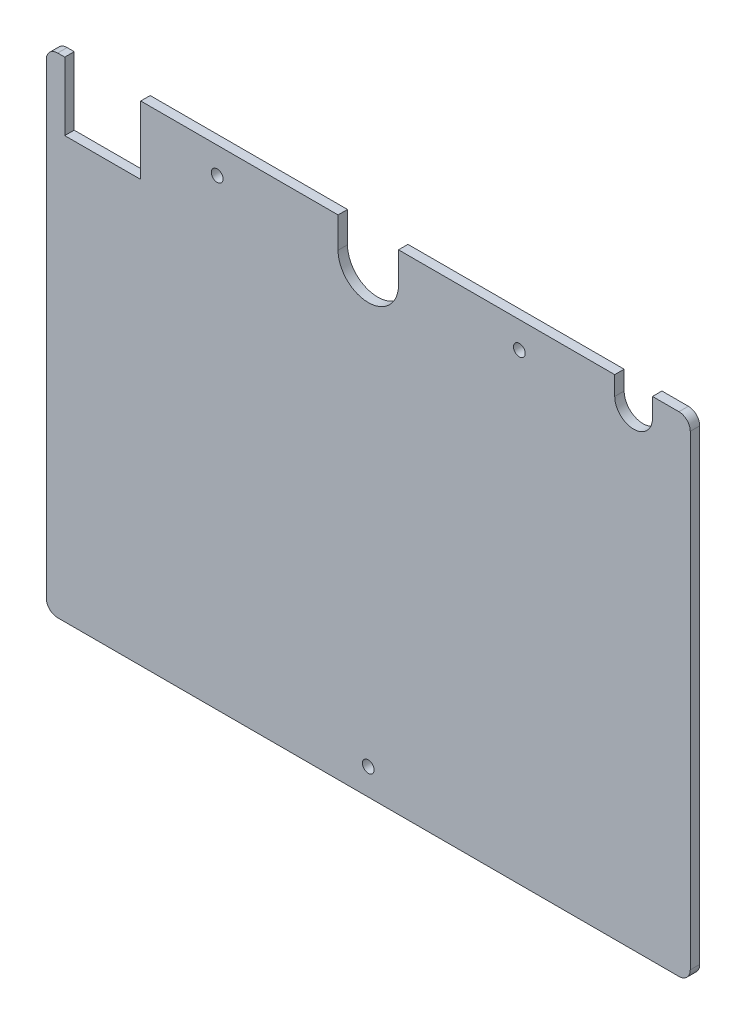
SolidWorks part; units mm, degrees
ref_plane "Plano frontal" through (0, 0, 0) normal (0, 0, 1) x (1, 0, 0)
ref_plane "Plano superior" through (0, 0, 0) normal (0, 1, 0) x (1, 0, 0)
ref_plane "Plano direito" through (0, 0, 0) normal (1, 0, 0) x (0, 0, -1)
sketch "Esboço1" plane through (0, 0, 0) normal (0, 0, 1) x (1, 0, 0)
  line L1 (-82.25, 64.75) -> (82.25, 64.75)
  line L2 (-85.25, 61.75) -> (-85.25, -61.75)
  line L3 (-82.25, -64.75) -> (82.25, -64.75)
  line L4 (85.25, 61.75) -> (85.25, -61.75)
  line L5 (-85.25, 64.75) -> (85.25, -64.75) construction
  line L6 (-85.25, -64.75) -> (85.25, 64.75) construction
  arc A0 (-85.25, -61.75) -> (-82.25, -64.75) centre (-82.25, -61.75) ccw
  arc A1 (82.25, -64.75) -> (85.25, -61.75) centre (82.25, -61.75) ccw
  arc A2 (82.25, 64.75) -> (85.25, 61.75) centre (82.25, 61.75) cw
  arc A3 (-82.25, 64.75) -> (-85.25, 61.75) centre (-82.25, 61.75) ccw
  point P0 (0, 0)
  dimension "D1" = 3
  dimension "D2" = 129.5
  dimension "D3" = 170.5
extrude "Ressalto-extrusão1" add sketch "Esboço1" along normal blind 2.5
sketch "Esboço2" plane through (0, 0, 2.5) normal (0, 0, 1) x (1, 0, 0)
  line L0 (8, 56.65) -> (8, 64.75)
  line L1 (82.25, 64.75) -> (-82.25, 64.75) construction
  line L2 (8, 64.75) -> (-8, 64.75)
  line L3 (-8, 64.75) -> (-8, 56.65)
  line L5 (-60.25, 64.75) -> (-80.3642, 64.75)
  line L6 (-60.25, 64.75) -> (-60.25, 46.75)
  line L7 (-60.25, 46.75) -> (-80.3642, 46.75)
  line L8 (-80.3642, 64.75) -> (-80.3642, 46.75)
  line L9 (85.25, -61.75) -> (85.25, 61.75) construction
  line L10 (65.25, 64.75) -> (75.25, 64.75)
  line L11 (65.25, 64.75) -> (65.25, 59.75)
  line L13 (75.25, 64.75) -> (75.25, 59.75)
  line L14 (-82.25, -64.75) -> (82.25, -64.75) construction
  line L15 (0, 0) -> (0, 27.1205) construction
  line L16 (-85.25, 61.75) -> (-85.25, -61.75) construction
  arc A0 (-8, 56.65) -> (8, 56.65) centre (0, 56.65) ccw
  arc A1 (65.25, 59.75) -> (75.25, 59.75) centre (70.25, 59.75) ccw
  circle A2 centre (0, -57.75) radius 1.55
  circle A3 centre (-40, 57.75) radius 1.55
  circle A4 centre (40, 57.75) radius 1.55
  dimension "D2" = 16
  dimension "D6" = 10
  dimension "D8" = 3.1
  dimension "D11" = 3.1
  dimension "D1" = 8.1
  dimension "D3" = 18
  dimension "D4" = 25
  dimension "D5" = 10
  dimension "D7" = 7
  dimension "D9" = 4.8858
  dimension "D10" = 7
  dimension "D12" = 80
extrude "Corte-extrusão1" cut sketch "Esboço2" against normal through all
